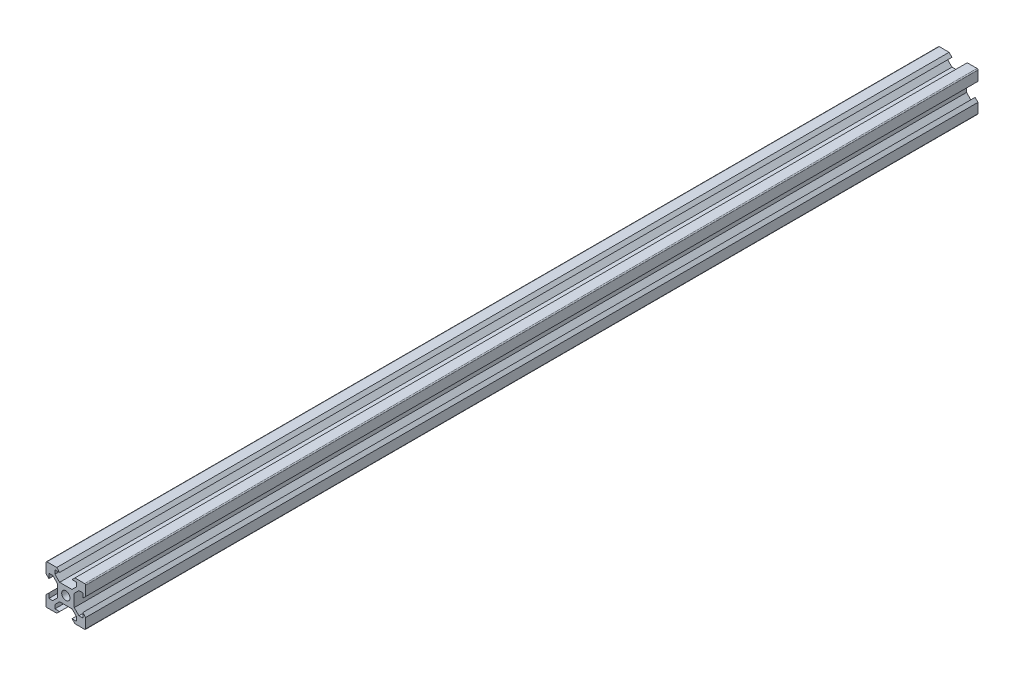
SolidWorks part; units mm, degrees
ref_plane "Front Plane" through (0, 0, 0) normal (0, 0, 1) x (1, 0, 0)
ref_plane "Top Plane" through (0, 0, 0) normal (0, 1, 0) x (1, 0, 0)
ref_plane "Right Plane" through (0, 0, 0) normal (1, 0, 0) x (0, 0, -1)
sketch "Sketch1" plane through (0, 0, 0) normal (0, 0, 1) x (1, 0, 0)
  line L0 (-3.125, 4.245) -> (3.125, 4.245)
  line L1 (3.125, 4.245) -> (5.5, 6.62)
  line L2 (5.5, 6.62) -> (5.5, 8.545)
  line L3 (5.5, 8.545) -> (3.125, 8.545)
  line L4 (3.125, 8.545) -> (4.58, 10)
  line L5 (4.58, 10) -> (9.5, 10)
  line L6 (10, 9.5) -> (10, 4.58)
  line L7 (10, 4.58) -> (8.545, 3.125)
  line L8 (8.545, 3.125) -> (8.545, 5.5)
  line L9 (8.545, 5.5) -> (6.62, 5.5)
  line L10 (6.62, 5.5) -> (4.245, 3.125)
  line L11 (4.245, 3.125) -> (4.245, -3.125)
  line L12 (0, 0) -> (-9.4136, 0) construction
  line L13 (0, 0) -> (0, -8.8273) construction
  line L14 (-4.245, 3.125) -> (-4.245, -3.125)
  line L15 (-6.62, 5.5) -> (-4.245, 3.125)
  line L16 (-8.545, 5.5) -> (-6.62, 5.5)
  line L17 (-8.545, 3.125) -> (-8.545, 5.5)
  line L18 (-10, 4.58) -> (-8.545, 3.125)
  line L19 (-10, 9.5) -> (-10, 4.58)
  line L20 (-4.58, 10) -> (-9.5, 10)
  line L21 (-3.125, 8.545) -> (-4.58, 10)
  line L22 (-5.5, 8.545) -> (-3.125, 8.545)
  line L23 (-5.5, 6.62) -> (-5.5, 8.545)
  line L24 (-3.125, 4.245) -> (-5.5, 6.62)
  line L25 (-3.125, -4.245) -> (-5.5, -6.62)
  line L26 (-5.5, -6.62) -> (-5.5, -8.545)
  line L27 (-5.5, -8.545) -> (-3.125, -8.545)
  line L28 (-3.125, -8.545) -> (-4.58, -10)
  line L29 (-4.58, -10) -> (-9.5, -10)
  line L30 (-10, -9.5) -> (-10, -4.58)
  line L31 (-10, -4.58) -> (-8.545, -3.125)
  line L32 (-8.545, -3.125) -> (-8.545, -5.5)
  line L33 (-8.545, -5.5) -> (-6.62, -5.5)
  line L34 (-6.62, -5.5) -> (-4.245, -3.125)
  line L35 (6.62, -5.5) -> (4.245, -3.125)
  line L36 (8.545, -5.5) -> (6.62, -5.5)
  line L37 (8.545, -3.125) -> (8.545, -5.5)
  line L38 (10, -4.58) -> (8.545, -3.125)
  line L39 (10, -9.5) -> (10, -4.58)
  line L40 (4.58, -10) -> (9.5, -10)
  line L41 (3.125, -8.545) -> (4.58, -10)
  line L42 (5.5, -8.545) -> (3.125, -8.545)
  line L43 (5.5, -6.62) -> (5.5, -8.545)
  line L44 (3.125, -4.245) -> (5.5, -6.62)
  line L45 (-3.125, -4.245) -> (3.125, -4.245)
  circle A0 centre (0, 0) radius 2.1
  arc A1 (10, 9.5) -> (9.5, 10) centre (9.5, 9.5) ccw
  arc A2 (-10, 9.5) -> (-9.5, 10) centre (-9.5, 9.5) cw
  arc A3 (-10, -9.5) -> (-9.5, -10) centre (-9.5, -9.5) ccw
  arc A4 (10, -9.5) -> (9.5, -10) centre (9.5, -9.5) cw
  point P3 (-10, 10)
  point P18 (10, 10)
  point P35 (0, 4.245)
  point P37 (4.245, 0)
  point P38 (-4.245, 0)
  point P62 (0, -4.245)
  point P63 (10, -10)
  point P64 (-10, -10)
  dimension "D1" = 4.2
  dimension "D17" = 0.5
  dimension "D2" = 10
  dimension "D3" = 10
  dimension "D4" = 45
  dimension "D5" = 3.125
  dimension "D6" = 3.125
  dimension "D7" = 4.58
  dimension "D8" = 4.58
  dimension "D9" = 5.5
  dimension "D10" = 5.5
  dimension "D13" = 3.125
  dimension "D14" = 3.125
  dimension "D15" = 4.3
  dimension "D16" = 4.3
extrude "Boss-Extrude1" add sketch "Sketch1" along normal blind 450
